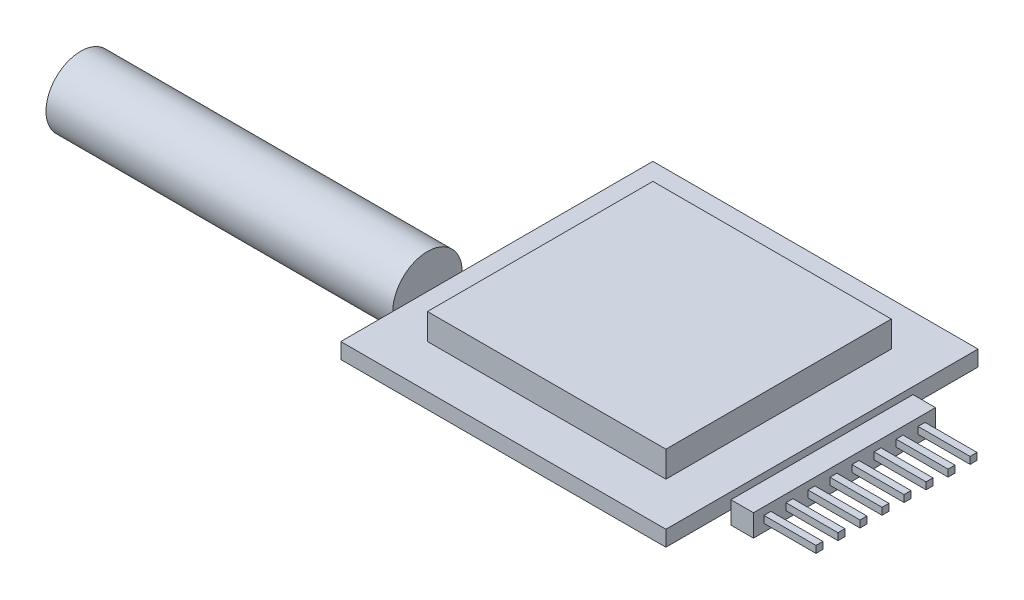
SolidWorks part; units mm, degrees
ref_plane "Alzado" through (0, 0, 0) normal (0, 0, 1) x (1, 0, 0)
ref_plane "Planta" through (0, 0, 0) normal (0, 1, 0) x (1, 0, 0)
ref_plane "Vista lateral" through (0, 0, 0) normal (1, 0, 0) x (0, 0, -1)
sketch "Croquis1" plane through (0, 0, 0) normal (0, 1, 0) x (1, 0, 0)
  line L1 (0, 0) -> (37.5, 0)
  line L2 (0, 0) -> (0, 36)
  line L3 (0, 36) -> (37.5, 36)
  line L4 (37.5, 0) -> (37.5, 36)
  dimension "D1" = 37.5
  dimension "D2" = 36
extrude "Saliente-Extruir1" add sketch "Croquis1" along normal blind 1.8
sketch "Croquis2" plane through (0, 1.8, 0) normal (0, 1, 0) x (1, 0, 0)
  line L0 (0, 36) -> (0, 0) construction
  line L1 (5, 5) -> (32.5, 5)
  line L2 (5, 5) -> (5, 31)
  line L3 (5, 31) -> (32.5, 31)
  line L4 (32.5, 5) -> (32.5, 31)
  line L5 (37.5, 36) -> (0, 36) construction
  line L6 (0, 0) -> (37.5, 0) construction
  line L7 (37.5, 0) -> (37.5, 36) construction
  dimension "D1" = 5
  dimension "D2" = 5
  dimension "5" = 5
  dimension "D4" = 5
extrude "Saliente-Extruir2" add sketch "Croquis2" along normal blind 3
sketch "Croquis3" plane through (37.5, 0, 0) normal (1, 0, 0) x (0, 0, -1)
  line L0 (0, 1.8) -> (36, 1.8) construction
  line L1 (7.5, 1) -> (28.5, 1)
  line L2 (7.5, 1) -> (7.5, -1.54)
  line L3 (7.5, -1.54) -> (28.5, -1.54)
  line L4 (28.5, 1) -> (28.5, -1.54)
  line L5 (5, 1.8) -> (31, 1.8) construction
  point P6 (18, 1)
  point P9 (18, 1.8)
  dimension "D1" = 2.54
  dimension "D2" = 0.8
  dimension "D3" = 21
extrude "Saliente-Extruir3" add sketch "Croquis3" along normal blind 2.6
sketch "Croquis4" plane through (40.1, 0, 0) normal (1, 0, 0) x (0, 0, -1)
  line L0 (17.13, 0.13) -> (16.33, -0.67) construction
  line L1 (21.41, 0.13) -> (21.41, -0.67)
  line L2 (18.87, 0.13) -> (19.67, 0.13)
  line L3 (18.87, 0.13) -> (18.87, -0.67)
  line L4 (18.87, -0.67) -> (19.67, -0.67)
  line L5 (19.67, 0.13) -> (19.67, -0.67)
  line L6 (18.87, 0.13) -> (19.67, -0.67) construction
  line L7 (18.87, -0.67) -> (19.67, 0.13) construction
  line L8 (21.41, 0.13) -> (22.21, 0.13)
  line L9 (22.21, 0.13) -> (22.21, -0.67)
  line L10 (21.41, -0.67) -> (22.21, -0.67)
  line L11 (16.33, 0.13) -> (17.13, 0.13)
  line L12 (17.13, 0.13) -> (17.13, -0.67)
  line L13 (16.33, -0.67) -> (17.13, -0.67)
  line L14 (16.33, 0.13) -> (16.33, -0.67)
  line L15 (23.95, 0.13) -> (23.95, -0.67)
  line L16 (23.95, 0.13) -> (24.75, 0.13)
  line L17 (24.75, 0.13) -> (24.75, -0.67)
  line L18 (23.95, -0.67) -> (24.75, -0.67)
  line L19 (26.49, 0.13) -> (26.49, -0.67)
  line L20 (26.49, 0.13) -> (27.29, 0.13)
  line L21 (27.29, 0.13) -> (27.29, -0.67)
  line L22 (26.49, -0.67) -> (27.29, -0.67)
  line L23 (13.79, 0.13) -> (14.59, 0.13)
  line L24 (14.59, 0.13) -> (14.59, -0.67)
  line L25 (13.79, -0.67) -> (14.59, -0.67)
  line L26 (13.79, 0.13) -> (13.79, -0.67)
  line L27 (11.25, 0.13) -> (12.05, 0.13)
  line L28 (12.05, 0.13) -> (12.05, -0.67)
  line L29 (11.25, -0.67) -> (12.05, -0.67)
  line L30 (11.25, 0.13) -> (11.25, -0.67)
  line L31 (8.71, 0.13) -> (9.51, 0.13)
  line L32 (9.51, 0.13) -> (9.51, -0.67)
  line L33 (8.71, -0.67) -> (9.51, -0.67)
  line L34 (8.71, 0.13) -> (8.71, -0.67)
  line L35 (16.73, -0.27) -> (19.27, -0.27) construction
  line L36 (18, -0.27) -> (18, 1) construction
  line L37 (28.5, 1) -> (7.5, 1) construction
  line L38 (7.5, 1) -> (7.5, -1.54) construction
  point P4 (19.27, -0.27)
  point P43 (7.5, -0.27)
  dimension "D1" = 0.8
  dimension "D2" = 0.8
  dimension "D3" = 4
  dimension "D4" = 5
extrude "Saliente-Extruir4" add sketch "Croquis4" along normal blind 6
sketch "Croquis5" plane through (0, 0, 0) normal (-1, 0, 0) x (0, 0, 1)
  line L0 (-36, 1.8) -> (0, 1.8) construction
  line L1 (0, 1.8) -> (0, 0) construction
  circle A0 centre (-10, 1.8) radius 4
  dimension "D1" = 8
  dimension "D2" = 10
extrude "Saliente-Extruir5" add sketch "Croquis5" along normal blind 40
